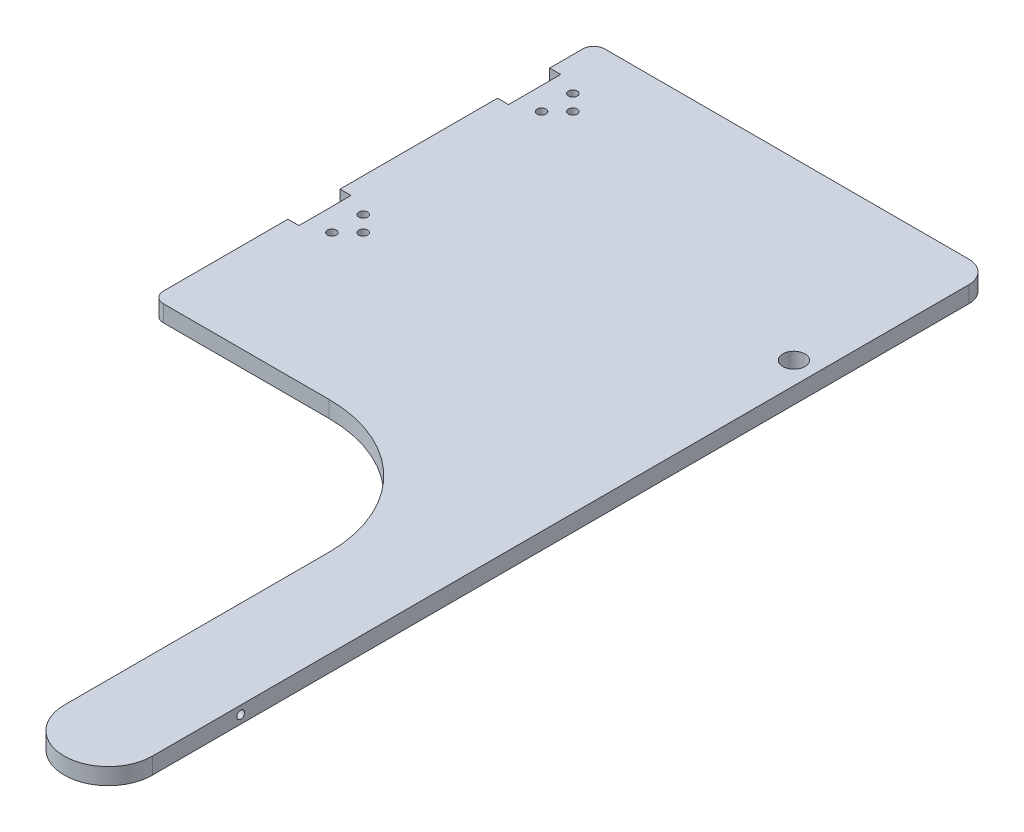
SolidWorks part; units mm, degrees
ref_plane "Front Plane" through (0, 0, 0) normal (0, 0, 1) x (1, 0, 0)
ref_plane "Top Plane" through (0, 0, 0) normal (0, 1, 0) x (1, 0, 0)
ref_plane "Right Plane" through (0, 0, 0) normal (1, 0, 0) x (0, 0, -1)
sketch "Sketch1" plane through (0, 0, 0) normal (0, 1, 0) x (1, 0, 0)
  line L1 (6.35, 0) -> (101.6, 0)
  line L2 (0, 6.35) -> (0, 247.65)
  line L3 (6.35, 254) -> (215.9, 254)
  line L6 (228.6, 241.3) -> (228.6, -228.6)
  line L8 (177.8, -76.2) -> (177.8, -228.6)
  arc A0 (177.8, -76.2) -> (101.6, 0) centre (101.6, -76.2) ccw
  arc A3 (228.6, 241.3) -> (215.9, 254) centre (215.9, 241.3) ccw
  arc A4 (0, 6.35) -> (6.35, 0) centre (6.35, 6.35) ccw
  arc A5 (0, 247.65) -> (6.35, 254) centre (6.35, 247.65) cw
  arc A6 (228.6, -228.6) -> (177.8, -228.6) centre (203.2, -228.6) cw
  point P17 (228.6, 254)
  point P20 (0, 0)
  point P23 (0, 254)
  dimension "D5" = 76.2
  dimension "D6" = 12.7
  dimension "D7" = 6.35
  dimension "D3" = 25.4
  dimension "D4" = 482.6
  dimension "D1" = 254
  dimension "D2" = 228.6
extrude "Boss-Extrude1" add sketch "Sketch1" along normal blind 9.525
sketch "Sketch2" plane through (0, 9.525, 0) normal (0, 1, 0) x (1, 0, 0)
  line L0 (0, 247.65) -> (0, 6.35) construction
  line L1 (0, 228.6) -> (6.35, 228.6)
  line L2 (0, 228.6) -> (0, 198.6)
  line L3 (0, 198.6) -> (6.35, 198.6)
  line L4 (6.35, 228.6) -> (6.35, 198.6)
  line L5 (215.9, 254) -> (6.35, 254) construction
  line L19 (6.35, 213.6) -> (63.5487, 213.6) construction
  line L28 (0, 107.95) -> (6.35, 107.95)
  line L33 (0, 107.95) -> (0, 77.95)
  line L34 (0, 77.95) -> (6.35, 77.95)
  line L35 (6.35, 107.95) -> (6.35, 77.95)
  line L36 (6.35, 92.95) -> (63.5487, 92.95) construction
  circle A1 centre (28.35, 213.6) radius 2.54
  circle A2 centre (19.35, 222.6) radius 2.54
  circle A3 centre (19.35, 204.6) radius 2.54
  circle A13 centre (28.35, 92.95) radius 2.54
  circle A14 centre (19.35, 101.95) radius 2.54
  circle A15 centre (19.35, 83.95) radius 2.54
  dimension "D3" = 28.35
  dimension "D4" = 5.08
  dimension "D5" = 19.35
  dimension "D6" = 9
  dimension "D1" = 30
  dimension "D2" = 25.4
  dimension "D7" = 2
  dimension "D8" = 6.35
  dimension "D9" = 120.65
extrude "Cut-Extrude1" cut sketch "Sketch2" against normal up to next
sketch "Sketch3" plane through (228.6, 0, 0) normal (1, 0, 0) x (0, 0, -1)
  line L0 (-254, 9.525) -> (-254, 0) construction
  line L1 (-228.6, 0) -> (241.3, 0) construction
  circle A0 centre (-177.8, 4.7625) radius 2.2479
  dimension "D2" = 4.4958
  dimension "D3" = 4.7625
  dimension "D1" = 76.2
extrude "Cut-Extrude2" cut sketch "Sketch3" against normal up to next
hole_wizard "#7 (0.201) Diameter Hole1" positions "Sketch5" profile "Sketch6" hole size "#7" standard "ANSI Inch"
sketch "Sketch5" plane through (0, 0, 0) normal (0, -1, 0) x (-1, 0, 0)
  line L0 (0, 153.275) -> (-228.6, 153.275) construction
  line L1 (0, 198.6) -> (0, 107.95) construction
  line L2 (-228.6, -228.6) -> (-228.6, 241.3) construction
  point P2 (-165.1, 143.75)
  point P16 (-165.1, 162.8)
  dimension "D1" = 19.05
  dimension "D2" = 63.5
sketch "Sketch6" plane through (165.1, 0, -143.75) normal (1, 0, 0) x (0, 0, -1)
  line L0 (0, 0) -> (0, 4.7088)
  line L1 (0, 4.7088) -> (2.5527, 3.175)
  line L2 (2.5527, 3.175) -> (2.5527, 0)
  line L5 (2.5527, 0) -> (0, 0)
  line L10 (0, 4.7088) -> (-2.5527, 3.175) construction
  line L11 (0, -6.35) -> (0, 107.95) construction
  dimension "Hole Dia." = 5.1054
  dimension "Hole Depth" = 3.175
  dimension "Drill Angle" = 118
sketch "Sketch7" plane through (0, 9.525, 0) normal (0, 1, 0) x (1, 0, 0)
  line L0 (0, 153.275) -> (228.6, 153.275) construction
  line L1 (0, 198.6) -> (0, 107.95) construction
  line L2 (228.6, -228.6) -> (228.6, 241.3) construction
  circle A0 centre (215.9, 153.275) radius 6.35
  point P8 (0, 0)
  dimension "D2" = 12.7
  dimension "D1" = 12.7
extrude "Cut-Extrude3" cut sketch "Sketch7" against normal through all
